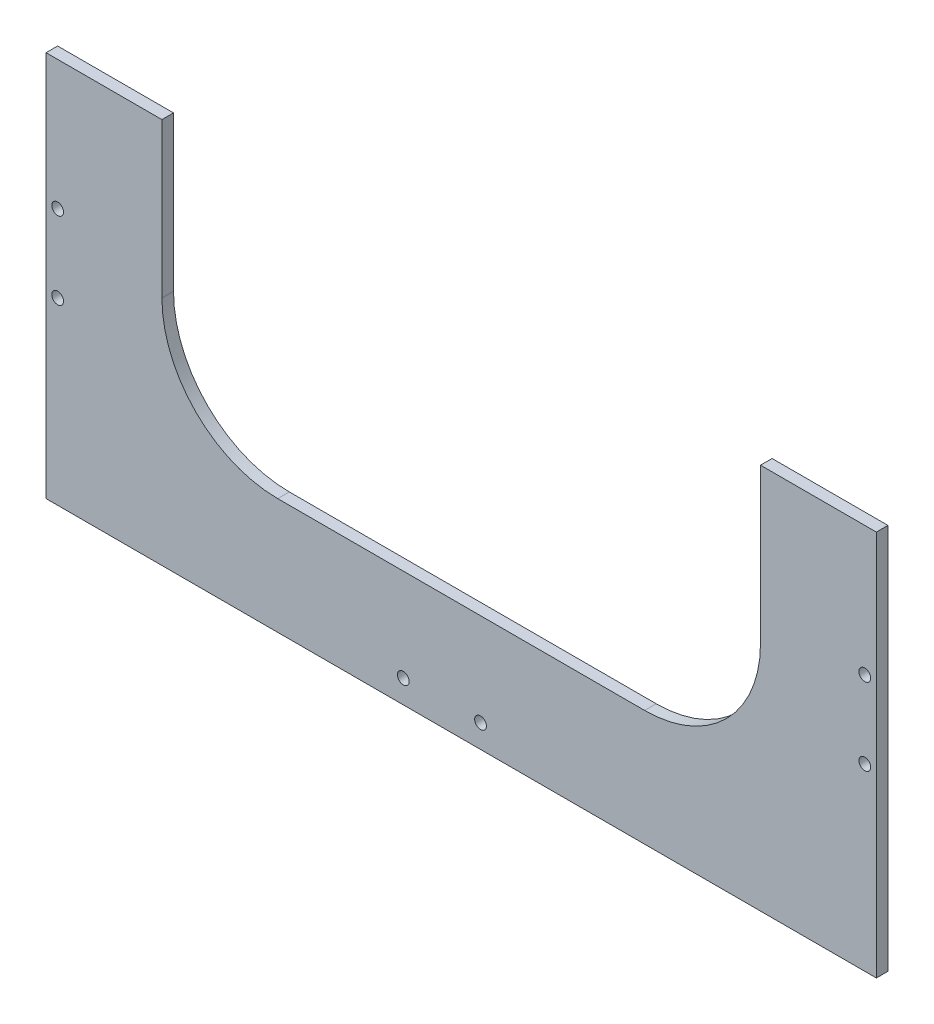
SolidWorks part; units mm, degrees
material "Thornel Mat VMA"
ref_plane "前视基准面" through (0, 0, 0) normal (0, 0, 1) x (1, 0, 0)
ref_plane "上视基准面" through (0, 0, 0) normal (0, 1, 0) x (1, 0, 0)
ref_plane "右视基准面" through (0, 0, 0) normal (1, 0, 0) x (0, 0, -1)
sketch "草图1" plane through (0, 0, 0) normal (0, 0, 1) x (1, 0, 0)
  line L1 (-107.5, -50) -> (107.5, -50)
  line L2 (-107.5, -50) -> (-107.5, 50)
  line L3 (-107.5, 50) -> (107.5, 50)
  line L4 (107.5, -50) -> (107.5, 50)
  line L5 (0, 50) -> (0, -50) construction
  line L6 (-107.5, 0) -> (107.5, 0) construction
  point P0 (0, 0)
  dimension "D1" = 215
  dimension "D2" = 100
extrude "凸台-拉伸1" add sketch "草图1" along normal mid plane 3
sketch "草图2" plane through (0, 0, 1.5) normal (0, 0, 1) x (1, 0, 0)
  line L0 (107.5, 50) -> (-107.5, 50) construction
  line L1 (-77.5, -20) -> (77.5, -20)
  line L2 (-77.5, -20) -> (-77.5, 120)
  line L3 (-77.5, 120) -> (77.5, 120)
  line L4 (77.5, -20) -> (77.5, 120)
  line L5 (0, 120) -> (0, -20) construction
  line L6 (-77.5, 50) -> (77.5, 50) construction
  line L7 (107.5, -50) -> (107.5, 50) construction
  line L8 (-107.5, -50) -> (107.5, -50) construction
  point P0 (0, 50)
  dimension "D1" = 30
  dimension "D2" = 30
extrude "切除-拉伸1" cut sketch "草图2" against normal mid plane 43
fillet "圆角1" radius 30 2 edges at (77.5, -20, 0) (-77.5, -20, 0)
sketch "草图3" plane through (0, 0, -1.5) normal (0, 0, -1) x (-1, 0, 0)
  circle A0 centre (15, -44) radius 1.25 construction
  circle A1 centre (-5, -44) radius 1.25 construction
  circle A2 centre (15, -44) radius 1.25 construction
  circle A3 centre (-5, -44) radius 1.25 construction
  circle A4 centre (-5, -44) radius 1.525
  circle A5 centre (15, -44) radius 1.525
  dimension "D1" = 3.05
extrude "切除-拉伸2" cut sketch "草图3" against normal blind 10
sketch "草图4" plane through (0, 0, 1.5) normal (0, 0, 1) x (1, 0, 0)
  circle A0 centre (-104.5, -3.5) radius 1.25 construction
  circle A1 centre (-104.5, 16.5) radius 1.25 construction
  circle A2 centre (-104.5, -3.5) radius 1.25 construction
  circle A3 centre (-104.5, 16.5) radius 1.25 construction
  circle A4 centre (-104.5, 16.5) radius 1.525
  circle A5 centre (-104.5, -3.5) radius 1.525
  dimension "D1" = 3.05
extrude "切除-拉伸3" cut sketch "草图4" against normal blind 10
sketch "草图5" [suppressed] plane through (0, 0, -1.5) normal (0, 0, -1) x (-1, 0, 0)
  circle A0 centre (104.5, -13.5) radius 1.25 construction
  circle A1 centre (104.5, 6.5) radius 1.25 construction
  circle A2 centre (104.5, -13.5) radius 1.25 construction
  circle A3 centre (104.5, 6.5) radius 1.25 construction
  circle A4 centre (104.5, 6.5) radius 1.525
  circle A5 centre (104.5, -13.5) radius 1.525
  dimension "D1" = 3.05
extrude "切除-拉伸4" [suppressed] cut sketch "草图5" against normal blind 10
mirror "镜向1" about plane through (0, 0, 0) normal (1, 0, 0) of "切除-拉伸3"
mirror "镜向2" [suppressed] about plane through (0, 0, 0) normal (1, 0, 0)
sketch "草图6" [suppressed] plane through (0, 0, 1.5) normal (0, 0, 1) x (1, 0, 0)
  line L0 (82.5, 43) -> (102.5, 43) construction
  line L1 (77.5, 30) -> (107.5, 30) construction
  line L2 (77.5, 50) -> (77.5, 10) construction
  line L3 (107.5, -50) -> (107.5, 50) construction
  line L4 (92.5, 30) -> (92.5, 43) construction
  line L5 (107.5, 50) -> (77.5, 50) construction
  circle A0 centre (82.5, 43) radius 1.525
  circle A1 centre (102.5, 43) radius 1.525
  dimension "D1" = 3.05
  dimension "D2" = 20
  dimension "D3" = 7
extrude "切除-拉伸5" [suppressed] cut sketch "草图6" against normal blind 10
